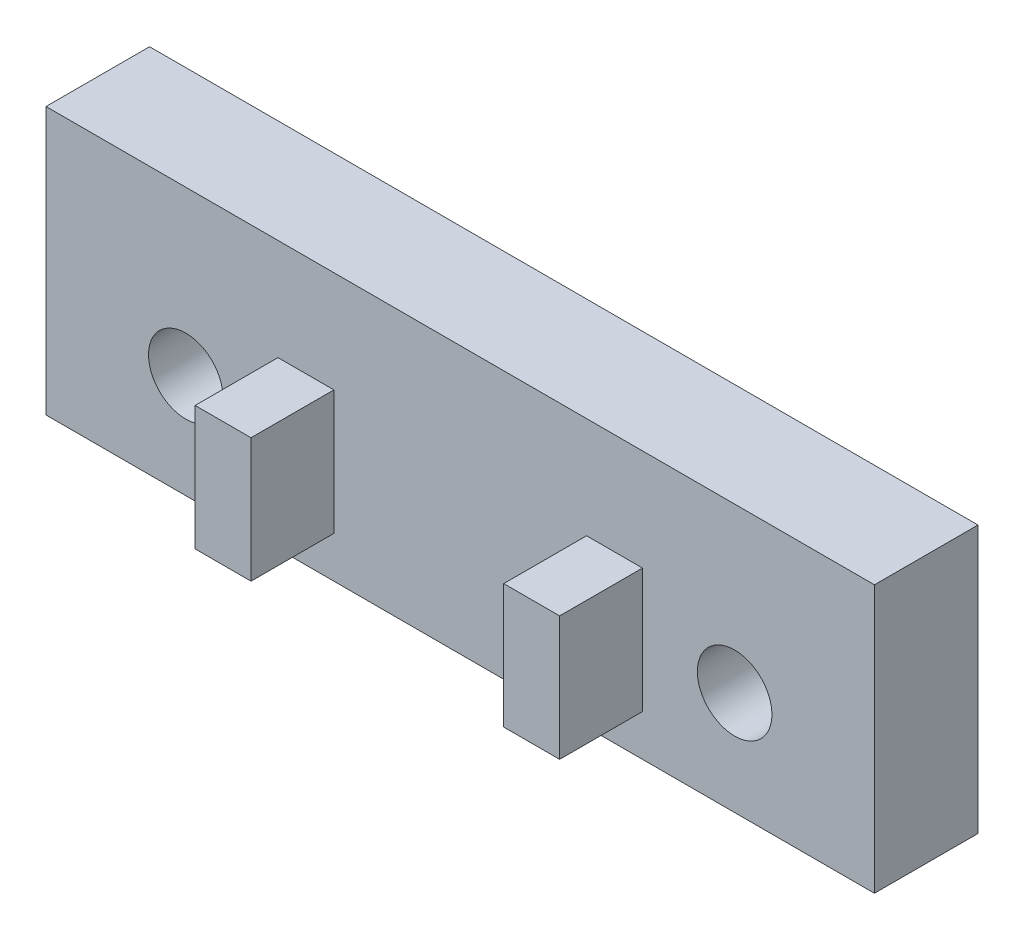
SolidWorks part; units mm, degrees
ref_plane "Front Plane" through (0, 0, 0) normal (0, 0, 1) x (1, 0, 0)
ref_plane "Top Plane" through (0, 0, 0) normal (0, 1, 0) x (1, 0, 0)
ref_plane "Right Plane" through (0, 0, 0) normal (1, 0, 0) x (0, 0, -1)
sketch "Sketch1" plane through (0, 0, 0) normal (0, 0, 1) x (1, 0, 0)
  line L1 (20, 5) -> (-20, 5)
  line L2 (20, 5) -> (20, -5)
  line L3 (20, -5) -> (-20, -5)
  line L4 (-20, 5) -> (-20, -5)
  line L5 (0, -5) -> (0, 5) construction
  line L6 (20, 0) -> (-20, 0) construction
  point P0 (0, 0)
  dimension "D1" = 10
  dimension "D2" = 40
extrude "Boss-Extrude1" add sketch "Sketch1" along normal blind 5
hole_wizard "M3 Clearance Hole1" positions "Sketch2" profile "Sketch3" hole size "M3" standard "ANSI Metric" end condition through all
sketch "Sketch2" plane through (0, 0, 0) normal (0, 0, 1) x (1, 0, 0)
  line L0 (-13.25, 0) -> (13.25, 0) construction
  point P0 (-13.25, 0)
  point P2 (13.25, 0)
  dimension "D1" = 26.5
sketch "Sketch3" plane through (-13.25, 0, 0) normal (1, 0, 0) x (0, 1, 0)
  line L0 (0, 0) -> (0, 5)
  line L1 (0, 5) -> (1.8, 5)
  line L2 (1.8, 5) -> (1.8, 0)
  line L5 (1.8, 0) -> (0, 0)
  line L11 (0, -6.35) -> (0, 107.95) construction
  dimension "Thru Hole Dia." = 3.6
  dimension "Thru Hole Depth" = 5
sketch "Sketch4" plane through (0, 0, 5) normal (0, 0, 1) x (1, 0, 0)
  line L0 (0, 0) -> (0, 5) construction
  line L1 (-8.8, 3) -> (-6.1, 3)
  line L2 (-8.8, 3) -> (-8.8, -3)
  line L3 (-8.8, -3) -> (-6.1, -3)
  line L4 (-6.1, 3) -> (-6.1, -3)
  line L5 (-7.45, -3) -> (-7.45, 3) construction
  line L6 (-8.8, 0) -> (-6.1, 0) construction
  line L7 (20, 5) -> (-20, 5) construction
  line L8 (8.8, 0) -> (6.1, 0) construction
  line L9 (7.45, -3) -> (7.45, 3) construction
  line L10 (6.1, 3) -> (6.1, -3)
  line L11 (8.8, -3) -> (6.1, -3)
  line L12 (8.8, 3) -> (8.8, -3)
  line L13 (8.8, 3) -> (6.1, 3)
  point P16 (7.45, 0)
  point P188 (-7.45, 0)
  dimension "D1" = 2.7
  dimension "D2" = 6
  dimension "D3" = 12.2
extrude "Boss-Extrude2" add sketch "Sketch4" along normal blind 4
sketch "Sketch5" plane through (0, 5, 0) normal (0, 1, 0) x (1, 0, 0)
  line L4 (20, 0) -> (-20, 0)
  line L5 (-20, 0) -> (-20, -5)
  line L6 (-20, -5) -> (20, -5)
  line L7 (20, -5) -> (20, 0)
  line L8 (20, 0) -> (-20, 0)
  line L9 (-20, 0) -> (-20, -5)
  line L10 (-20, -5) -> (20, -5)
  line L11 (20, -5) -> (20, 0)
  dimension "D1" = 0
extrude "Boss-Extrude3" add sketch "Sketch5" along normal blind 2.9
